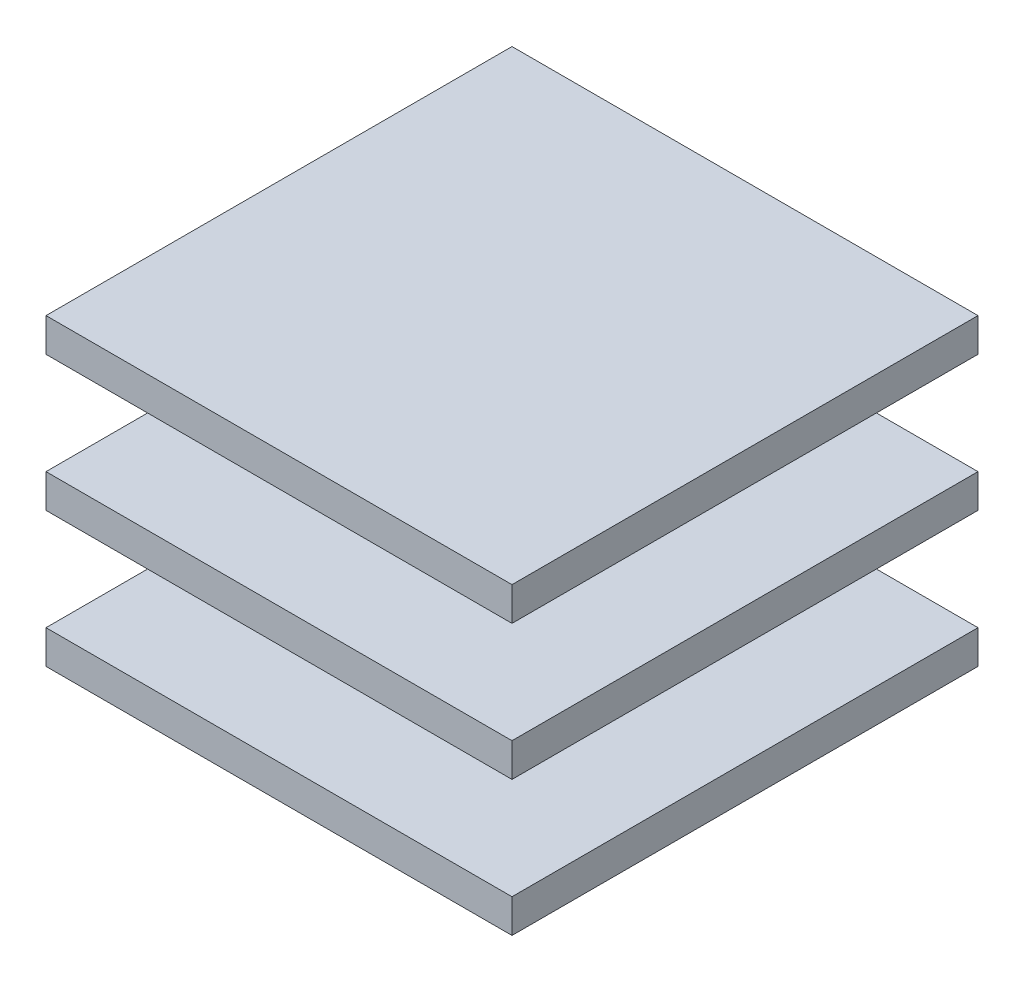
SolidWorks part; units mm, degrees
ref_plane "Face" through (0, 0, 0) normal (0, 0, 1) x (1, 0, 0)
ref_plane "Dessus" through (0, 0, 0) normal (0, 1, 0) x (1, 0, 0)
ref_plane "Droite" through (0, 0, 0) normal (1, 0, 0) x (0, 0, -1)
sketch "Esquisse1" plane through (0, 0, 0) normal (0, 1, 0) x (1, 0, 0)
  line L1 (0, 0) -> (250, 0)
  line L2 (0, 0) -> (0, 250)
  line L3 (0, 250) -> (250, 250)
  line L4 (250, 0) -> (250, 250)
  dimension "D1" = 250
extrude "Extrusion1" add sketch "Esquisse1" along normal blind 18
sketch "Esquisse2" plane through (0, 18, 0) normal (0, 1, 0) x (-1, 0, 0)
  line L0 (-125, -250) -> (-125, 0) construction
  line L1 (-250, -250) -> (0, -250) construction
  line L2 (0, 0) -> (-250, 0) construction
  line L3 (0, -125) -> (-250, -125) construction
  line L4 (0, -250) -> (0, 0) construction
  line L5 (-250, 0) -> (-250, -250) construction
  line L6 (-90, -160) -> (-160, -160)
  line L7 (-90, -90) -> (-160, -90)
  line L8 (-90, -90) -> (-90, -160)
  line L9 (-160, -90) -> (-160, -160)
  point P17 (-90, -125)
  point P18 (-125, -90)
  point P19 (-125, -160)
  dimension "D1" = 90
  dimension "D2" = 90
extrude "Extrusion2" add sketch "Esquisse2" along normal blind 54.5
sketch "Esquisse3" plane through (0, 72.5, 0) normal (0, 1, 0) x (1, 0, 0)
  line L1 (0, 0) -> (250, 0)
  line L2 (0, 0) -> (0, 250)
  line L3 (0, 250) -> (250, 250)
  line L4 (250, 0) -> (250, 250)
extrude "Extrusion3" add sketch "Esquisse3" along normal blind 18
sketch "Esquisse4" plane through (0, 90.5, 0) normal (0, 1, 0) x (1, 0, 0)
  line L0 (125, 250) -> (125, 0) construction
  line L1 (250, 250) -> (0, 250) construction
  line L2 (0, 0) -> (250, 0) construction
  line L3 (0, 125) -> (250, 125) construction
  line L4 (0, 250) -> (0, 0) construction
  line L5 (250, 0) -> (250, 250) construction
  line L7 (90, 90) -> (160, 90)
  line L8 (90, 90) -> (90, 160)
  line L9 (90, 160) -> (160, 160)
  line L10 (160, 90) -> (160, 160)
  dimension "D1" = 90
  dimension "D2" = 90
  dimension "D3" = 90
  dimension "D4" = 90
extrude "Extrusion4" add sketch "Esquisse4" along normal blind 54.5
sketch "Esquisse5" plane through (0, 145, 0) normal (0, 1, 0) x (1, 0, 0)
  line L1 (0, 0) -> (250, 0)
  line L2 (0, 0) -> (0, 250)
  line L3 (0, 250) -> (250, 250)
  line L4 (250, 0) -> (250, 250)
extrude "Extrusion5" add sketch "Esquisse5" along normal blind 18
